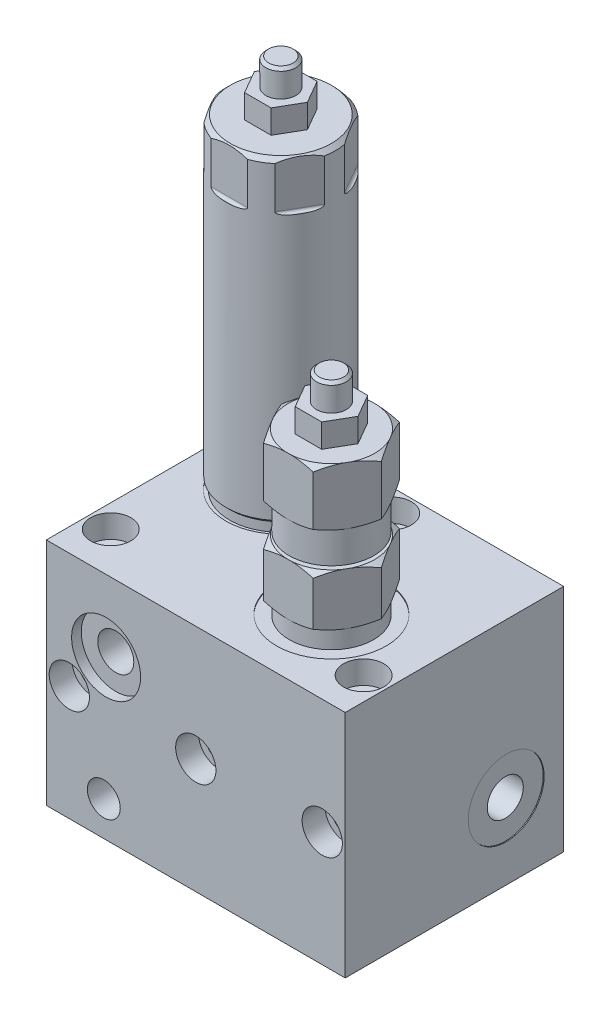
SolidWorks part; units mm, degrees
material "Alloy Steel"
ref_plane "Front Plane" through (0, 0, 0) normal (0, 0, 1) x (1, 0, 0)
ref_plane "Top Plane" through (0, 0, 0) normal (0, 1, 0) x (1, 0, 0)
ref_plane "Right Plane" through (0, 0, 0) normal (1, 0, 0) x (0, 0, -1)
sketch "Sketch1" plane through (0, 0, 0) normal (0, 1, 0) x (1, 0, 0)
  line L1 (-41.275, -30.1625) -> (41.275, -30.1625)
  line L2 (-41.275, -30.1625) -> (-41.275, 30.1625)
  line L3 (-41.275, 30.1625) -> (41.275, 30.1625)
  line L4 (41.275, -30.1625) -> (41.275, 30.1625)
  line L5 (-41.275, -30.1625) -> (41.275, 30.1625) construction
  line L6 (-41.275, 30.1625) -> (41.275, -30.1625) construction
  circle A0 centre (0, 23.8125) radius 3.5687
  circle A1 centre (-34.925, -18.7325) radius 3.5687
  circle A2 centre (34.925, -18.7325) radius 3.5687
  point P0 (0, 0)
  dimension "D3" = 7.1374
  dimension "D1" = 60.325
  dimension "D2" = 82.55
  dimension "D4" = 6.35
  dimension "D5" = 11.43
  dimension "D6" = 6.35
  dimension "D7" = 6.35
extrude "Boss-Extrude1" add sketch "Sketch1" along normal blind 63.5
sketch "Sketch2" plane through (0, 63.5, 0) normal (0, 1, 0) x (1, 0, 0)
  circle A0 centre (-34.925, -18.7325) radius 5.5626
  circle A1 centre (0, 23.8125) radius 5.5626
  circle A2 centre (34.925, -18.7325) radius 5.5626
  dimension "D1" = 11.1252
extrude "Cut-Extrude1" cut sketch "Sketch2" against normal blind 6.35
sketch "Sketch3" plane through (0, 0, 30.1625) normal (0, 0, 1) x (1, 0, 0)
  line L0 (-41.275, 0) -> (41.275, 0) construction
  line L1 (-41.275, 63.5) -> (-41.275, 0) construction
  line L2 (41.275, 63.5) -> (41.275, 0) construction
  circle A0 centre (-34.925, 31.75) radius 3.5687
  circle A1 centre (0, 31.75) radius 3.5687
  circle A2 centre (34.925, 31.75) radius 3.5687
  dimension "D2" = 7.1374
  dimension "D1" = 31.75
  dimension "D3" = 6.35
  dimension "D4" = 6.35
extrude "Cut-Extrude2" cut sketch "Sketch3" against normal through all
sketch "Sketch4" plane through (0, 0, 30.1625) normal (0, 0, 1) x (1, 0, 0)
  circle A0 centre (-34.925, 31.75) radius 5.5626
  circle A1 centre (0, 31.75) radius 5.5626
  circle A2 centre (34.925, 31.75) radius 5.5626
  dimension "D1" = 11.1252
extrude "Cut-Extrude3" cut sketch "Sketch4" against normal blind 6.35
sketch "Sketch5" plane through (0, 0, 30.1625) normal (0, 0, 1) x (1, 0, 0)
  line L0 (41.275, 63.5) -> (41.275, 0) construction
  line L1 (-41.275, 0) -> (41.275, 0) construction
  circle A0 centre (-24.765, 43.688) radius 9.525
  dimension "D3" = 19.05
  dimension "D1" = 66.04
  dimension "D2" = 43.688
extrude "Cut-Extrude4" cut sketch "Sketch5" against normal blind 2.667 contours A0
sketch "Sketch7" plane through (0, 0, 30.1625) normal (0, 0, 1) x (1, 0, 0)
  line L0 (41.275, 63.5) -> (41.275, 0) construction
  line L1 (-41.275, 0) -> (41.275, 0) construction
  circle A0 centre (-24.765, 43.688) radius 4.9784
  dimension "D3" = 9.9568
  dimension "D1" = 66.04
  dimension "D2" = 43.688
extrude "Cut-Extrude5" cut sketch "Sketch7" against normal blind 20.32
sketch "Sketch8" plane through (0, 0, 30.1625) normal (0, 0, 1) x (1, 0, 0)
  line L0 (41.275, 63.5) -> (41.275, 0) construction
  line L1 (-41.275, 0) -> (41.275, 0) construction
  circle A0 centre (-25.4, 9.525) radius 4.5466
  dimension "D1" = 9.0932
  dimension "D2" = 66.675
  dimension "D3" = 9.525
extrude "Cut-Extrude6" cut sketch "Sketch8" against normal blind 10.668
sketch "Sketch9" plane through (0, 0, 0) normal (0, -1, 0) x (1, 0, 0)
  line L0 (-41.275, 30.1625) -> (41.275, 30.1625) construction
  line L1 (41.275, 30.1625) -> (41.275, -30.1625) construction
  circle A0 centre (-25.4, 7.3025) radius 7.9375
  circle A1 centre (26.67, -10.4775) radius 7.9375
  dimension "D5" = 15.875
  dimension "D1" = 22.86
  dimension "D2" = 66.675
  dimension "D3" = 40.64
  dimension "D4" = 14.605
extrude "Cut-Extrude7" cut sketch "Sketch9" against normal blind 2.667
sketch "Sketch10" plane through (0, 0, 0) normal (0, -1, 0) x (1, 0, 0)
  circle A0 centre (-25.4, 7.3025) radius 4.5466
  circle A1 centre (26.67, -10.4775) radius 4.5466
  dimension "D1" = 9.0932
extrude "Cut-Extrude8" cut sketch "Sketch10" against normal blind 12.7
sketch "Sketch11" plane through (41.275, 0, 0) normal (1, 0, 0) x (0, 0, -1)
  line L0 (-30.1625, 63.5) -> (-30.1625, 0) construction
  line L1 (-30.1625, 0) -> (30.1625, 0) construction
  circle A0 centre (14.2875, 20.828) radius 10.4775
  dimension "D3" = 20.955
  dimension "D1" = 44.45
  dimension "D2" = 20.828
extrude "Cut-Extrude11" cut sketch "Sketch11" against normal blind 0.254
sketch "Sketch12" plane through (41.275, 0, 0) normal (1, 0, 0) x (0, 0, -1)
  line L0 (-30.1625, 0) -> (30.1625, 0) construction
  line L1 (-30.1625, 63.5) -> (-30.1625, 0) construction
  circle A0 centre (14.2875, 20.828) radius 4.9784
  dimension "D1" = 9.9568
  dimension "D2" = 20.828
  dimension "D3" = 44.45
extrude "Cut-Extrude10" cut sketch "Sketch12" against normal blind 17.78
sketch "Sketch13" plane through (-41.275, 0, 0) normal (-1, 0, 0) x (0, 0, 1)
  line L0 (30.1625, 63.5) -> (30.1625, 0) construction
  line L1 (-30.1625, 0) -> (30.1625, 0) construction
  circle A0 centre (7.3025, 21.336) radius 10.4775
  dimension "D3" = 20.955
  dimension "D1" = 22.86
  dimension "D2" = 21.336
extrude "Cut-Extrude12" cut sketch "Sketch13" against normal blind 0.254
sketch "Sketch14" plane through (-41.275, 0, 0) normal (-1, 0, 0) x (0, 0, 1)
  circle A0 centre (7.3025, 21.336) radius 4.9784
  dimension "D1" = 9.9568
extrude "Cut-Extrude13" cut sketch "Sketch14" against normal blind 13.97
sketch "Sketch15" plane through (0, 0, -30.1625) normal (0, 0, -1) x (-1, 0, 0)
  line L0 (-41.275, 0) -> (41.275, 0) construction
  line L1 (-41.275, 63.5) -> (-41.275, 0) construction
  circle A0 centre (-25.4, 9.525) radius 7.9375
  circle A1 centre (25.4, 9.525) radius 7.9375
  circle A2 centre (-15.875, 51.3588) radius 10.4775
  dimension "D4" = 15.875
  dimension "D7" = 20.955
  dimension "D1" = 9.525
  dimension "D2" = 15.875
  dimension "D3" = 66.675
  dimension "D5" = 51.3588
  dimension "D6" = 25.4
extrude "Cut-Extrude14" cut sketch "Sketch15" against normal blind 2.667
sketch "Sketch16" plane through (0, 0, -30.1625) normal (0, 0, -1) x (-1, 0, 0)
  circle A0 centre (-15.875, 51.3588) radius 4.9784
  circle A1 centre (-25.4, 9.525) radius 3.4544
  circle A2 centre (25.4, 9.525) radius 3.4544
  dimension "D1" = 6.9088
  dimension "D2" = 9.9568
extrude "Cut-Extrude15" cut sketch "Sketch16" against normal blind 15.24
ref_plane "Plane1" through (0, 0, 8.5725) normal (0, 0, 1) x (1, 0, 0)
ref_plane "Plane2" through (0, 0, -14.2875) normal (0, 0, 1) x (1, 0, 0)
sketch "Sketch18" plane through (0, 63.5, 0) normal (0, 1, 0) x (1, 0, 0)
  line L0 (41.275, -30.1625) -> (41.275, 30.1625) construction
  line L1 (-41.275, -30.1625) -> (41.275, -30.1625) construction
  circle A0 centre (15.875, -8.5725) radius 15.1511
  circle A1 centre (-20.955, 14.2875) radius 15.1511
  dimension "D1" = 30.3022
  dimension "D6" = 30.3022
  dimension "D2" = 25.4
  dimension "D3" = 21.59
  dimension "D4" = 62.23
  dimension "D5" = 44.45
extrude "Cut-Extrude16" cut sketch "Sketch18" against normal blind 0.254
sketch "Sketch19" plane through (0, 0, 8.5725) normal (0, 0, 1) x (1, 0, 0)
  line L0 (15.875, 49.9044) -> (15.875, 88.0342) construction
  line L1 (41.275, 63.5) -> (41.275, 0) construction
  line L2 (15.875, 63.246) -> (27.5336, 63.246)
  line L3 (27.5336, 63.246) -> (27.5336, 68.072)
  line L4 (27.5336, 68.072) -> (29.6545, 69.2965)
  line L5 (29.6545, 69.2965) -> (29.6545, 81.4868)
  line L6 (29.6545, 81.4868) -> (27.813, 82.55)
  line L7 (27.813, 82.55) -> (24.384, 82.55)
  line L8 (24.384, 82.55) -> (24.384, 83.312)
  line L9 (24.384, 83.312) -> (27.5336, 83.312)
  line L10 (27.5336, 83.312) -> (27.5336, 91.948)
  line L11 (27.5336, 91.948) -> (29.6545, 93.1725)
  line L12 (29.6545, 93.1725) -> (29.6545, 106.8868)
  line L13 (29.6545, 106.8868) -> (27.813, 107.95)
  line L14 (27.813, 107.95) -> (20.0025, 107.95)
  line L15 (20.0025, 107.95) -> (20.0025, 121.158)
  line L16 (20.0025, 121.158) -> (19.2405, 121.92)
  line L17 (19.2405, 121.92) -> (15.875, 121.92)
  line L18 (15.875, 121.92) -> (15.875, 63.246)
  line L19 (31.0261, 63.246) -> (0.7239, 63.246) construction
  point P24 (17.5578, 121.92)
  dimension "D1" = 25.4
  dimension "D2" = 27.559
  dimension "D3" = 23.3172
  dimension "D4" = 60
  dimension "D5" = 30
  dimension "D6" = 0.762
  dimension "D7" = 17.018
  dimension "D8" = 8.636
  dimension "D9" = 14.478
  dimension "D10" = 19.304
  dimension "D11" = 23.876
  dimension "D12" = 23.3172
  dimension "D13" = 60
  dimension "D14" = 16.002
  dimension "D15" = 30
  dimension "D16" = 23.876
  dimension "D17" = 8.255
  dimension "D18" = 13.97
  dimension "D19" = 6.731
  dimension "D20" = 45
revolve "Revolve1" add sketch "Sketch19" angle 360 about L0
sketch "Sketch20" plane through (0, 107.95, 0) normal (0, 1, 0) x (1, 0, 0)
  line L1 (22.7527, 3.3401) -> (8.9973, 3.3401)
  line L2 (8.9973, 3.3401) -> (2.1195, -8.5725)
  line L3 (2.1195, -8.5725) -> (8.9973, -20.4851)
  line L4 (8.9973, -20.4851) -> (22.7527, -20.4851)
  line L5 (22.7527, -20.4851) -> (29.6305, -8.5725)
  line L6 (29.6305, -8.5725) -> (22.7527, 3.3401)
  circle A0 centre (15.875, -8.5725) radius 11.9126 construction
  circle A1 centre (15.875, -8.5725) radius 16.8275
  dimension "D2" = 33.655
  dimension "D1" = 23.8252
extrude "Cut-Extrude17" cut sketch "Sketch20" against normal blind 40.64
sketch "Sketch21" plane through (0, 107.95, 0) normal (0, 1, 0) x (1, 0, 0)
  line L1 (19.5412, -2.2225) -> (12.2088, -2.2225)
  line L2 (12.2088, -2.2225) -> (8.5427, -8.5725)
  line L3 (8.5427, -8.5725) -> (12.2088, -14.9225)
  line L4 (12.2088, -14.9225) -> (19.5412, -14.9225)
  line L5 (19.5412, -14.9225) -> (23.2073, -8.5725)
  line L6 (23.2073, -8.5725) -> (19.5412, -2.2225)
  circle A0 centre (15.875, -8.5725) radius 6.35 construction
  dimension "D1" = 12.7
extrude "Boss-Extrude3" add sketch "Sketch21" along normal blind 6.5532
sketch "Sketch22" plane through (0, 0, -14.2875) normal (0, 0, 1) x (1, 0, 0)
  line L0 (-20.955, 155.6049) -> (-20.955, 34.9582) construction
  line L2 (41.275, 63.5) -> (41.275, 0) construction
  line L3 (-20.955, 63.246) -> (-6.7945, 63.246)
  line L4 (-6.7945, 63.246) -> (-6.7945, 65.786)
  line L5 (-6.7945, 65.786) -> (-5.8674, 66.7131)
  line L6 (-5.8674, 66.7131) -> (-5.8674, 152.0698)
  line L7 (-5.8674, 152.0698) -> (-7.0104, 153.2128)
  line L8 (-7.0104, 153.2128) -> (-16.8275, 153.2128)
  line L9 (-16.8275, 153.2128) -> (-16.8275, 166.4208)
  line L10 (-16.8275, 166.4208) -> (-17.5895, 167.1828)
  line L11 (-17.5895, 167.1828) -> (-20.955, 167.1828)
  line L12 (-20.955, 167.1828) -> (-20.955, 63.246)
  line L13 (-5.8039, 63.246) -> (-36.1061, 63.246) construction
  circle A0 centre (-24.765, 43.688) radius 9.525 construction
  dimension "D1" = 62.23
  dimension "D2" = 2.54
  dimension "D3" = 45
  dimension "D4" = 28.321
  dimension "D5" = 30.1752
  dimension "D6" = 89.9668
  dimension "D7" = 45
  dimension "D8" = 1.143
  dimension "D9" = 13.97
  dimension "D10" = 45
  dimension "D11" = 8.255
  dimension "D12" = 6.731
revolve "Revolve2" add sketch "Sketch22" angle 360 about L0
sketch "Sketch23" plane through (0, 153.2128, 0) normal (0, 1, 0) x (1, 0, 0)
  line L1 (-29.1672, 0.0635) -> (-12.7428, 0.0635)
  line L2 (-12.7428, 0.0635) -> (-4.5305, 14.2875)
  line L3 (-4.5305, 14.2875) -> (-12.7428, 28.5115)
  line L4 (-12.7428, 28.5115) -> (-29.1672, 28.5115)
  line L5 (-29.1672, 28.5115) -> (-37.3795, 14.2875)
  line L6 (-37.3795, 14.2875) -> (-29.1672, 0.0635)
  circle A0 centre (-20.955, 14.2875) radius 14.224 construction
  circle A1 centre (-20.955, 14.2875) radius 17.145
  dimension "D2" = 34.29
  dimension "D1" = 28.448
extrude "Cut-Extrude18" cut sketch "Sketch23" against normal blind 13.462
fillet "Fillet1" radius 0.762 6 edges at (-33.2733, 139.7508, -7.1755) (-20.955, 139.7508, -0.0635) (-8.6367, 139.7508, -7.1755) (-8.6367, 139.7508, -21.3995) (-33.2733, 139.7508, -21.3995) (-20.955, 139.7508, -28.5115)
sketch "Sketch24" plane through (0, 153.2128, 0) normal (0, 1, 0) x (1, 0, 0)
  line L1 (-24.6212, 7.9375) -> (-17.2888, 7.9375)
  line L2 (-17.2888, 7.9375) -> (-13.6227, 14.2875)
  line L3 (-13.6227, 14.2875) -> (-17.2888, 20.6375)
  line L4 (-17.2888, 20.6375) -> (-24.6212, 20.6375)
  line L5 (-24.6212, 20.6375) -> (-28.2873, 14.2875)
  line L6 (-28.2873, 14.2875) -> (-24.6212, 7.9375)
  circle A0 centre (-20.955, 14.2875) radius 6.35 construction
  dimension "D1" = 12.7
extrude "Boss-Extrude4" add sketch "Sketch24" along normal blind 6.5532
